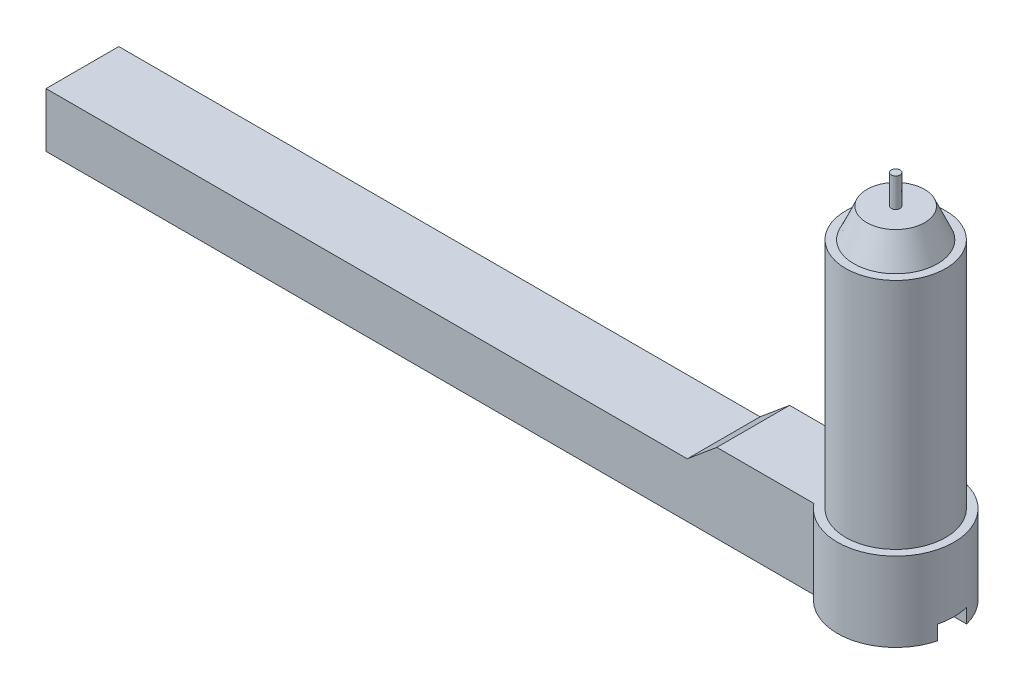
SolidWorks part; units mm, degrees
ref_plane "Front Plane" through (0, 0, 0) normal (0, 0, 1) x (1, 0, 0)
ref_plane "Top Plane" through (0, 0, 0) normal (0, 1, 0) x (1, 0, 0)
ref_plane "Right Plane" through (0, 0, 0) normal (1, 0, 0) x (0, 0, -1)
sketch "Sketch1" plane through (0, 0, 0) normal (0, 1, 0) x (1, 0, 0)
  line L1 (-42.6479, 3.8062) -> (10.0915, 3.8062)
  line L2 (-42.6479, 3.8062) -> (-42.6479, -1.1938)
  line L3 (-42.6479, -1.1938) -> (10.0915, -1.1938)
  arc A1 (10.0915, -1.1938) -> (10.0915, 3.8062) centre (13.214, 1.3062) ccw
  dimension "D2" = 8
  dimension "D1" = 5
extrude "Boss-Extrude1" add sketch "Sketch1" along normal blind 9
sketch "Sketch2" plane through (0, 0, 1.1938) normal (0, 0, 1) x (1, 0, 0)
  line L0 (1.398, 7.3049) -> (3.4266, 9)
  line L1 (-42.6479, 9) -> (1.398, 9)
  line L2 (-42.6479, 9) -> (-42.6479, 7.3049)
  line L3 (-42.6479, 7.3049) -> (1.398, 7.3049)
  line L5 (-42.6479, 9) -> (10.0915, 9) construction
  line L6 (1.398, 9) -> (3.4266, 9)
extrude "Cut-Extrude1" cut sketch "Sketch2" against normal blind 6
sketch "Sketch3" plane through (0, 9, 0) normal (0, 1, 0) x (1, 0, 0)
  circle A0 centre (13.214, 1.3062) radius 3.435
extrude "Boss-Extrude2" add sketch "Sketch3" along normal blind 16
sketch "Sketch4" plane through (0, 25, 0) normal (0, 1, 0) x (1, 0, 0)
  circle A0 centre (13.214, 1.3062) radius 2.8727
extrude "Boss-Extrude3" add sketch "Sketch4" along normal blind 2 draft 24
sketch "Sketch5" plane through (0, 27, 0) normal (0, 1, 0) x (1, 0, 0)
  circle A0 centre (13.214, 1.3062) radius 0.3
extrude "Boss-Extrude4" add sketch "Sketch5" along normal blind 2
sketch "Sketch6" plane through (0, 0, 1.1938) normal (0, 0, 1) x (1, 0, 0)
  line L0 (17.214, 0) -> (17.214, 9) construction
  line L1 (-42.6479, 0) -> (17.214, 0)
  line L2 (-42.6479, 0) -> (-42.6479, 3.5678)
  line L3 (-42.6479, 3.5678) -> (17.214, 3.5678)
  line L4 (17.214, 0) -> (17.214, 3.5678)
extrude "Cut-Extrude2" cut sketch "Sketch6" against normal through all both and the other way through all
sketch "Sketch7" plane through (0, 3.5678, 0) normal (0, -1, 0) x (1, 0, 0)
  line L0 (-42.6479, -1.3062) -> (-34.3543, -1.3062) construction
  line L1 (-42.6479, -3.8062) -> (-42.6479, 1.1938) construction
  circle A0 centre (-39.2201, -1.3062) radius 1
extrude "Cut-Extrude3" cut sketch "Sketch7" against normal blind 3
ref_plane "Plane1" through (26, 0, 0) normal (1, 0, 0) x (0, 0, -1)
sketch "Sketch8" plane through (26, 0, 0) normal (1, 0, 0) x (0, 0, -1)
  line L0 (1.3062, 3.5678) -> (1.3062, 12.1356) construction
  line L1 (-2.6938, 3.5678) -> (5.3062, 3.5678) construction
  line L3 (0.3062, 3.5678) -> (2.3062, 3.5678)
  line L4 (0.3062, 3.5678) -> (0.3062, 4.5678)
  line L5 (0.3062, 4.5678) -> (2.3062, 4.5678)
  line L6 (2.3062, 3.5678) -> (2.3062, 4.5678)
  dimension "D1" = 1
extrude "Cut-Extrude4" cut sketch "Sketch8" against normal blind 10.0001
